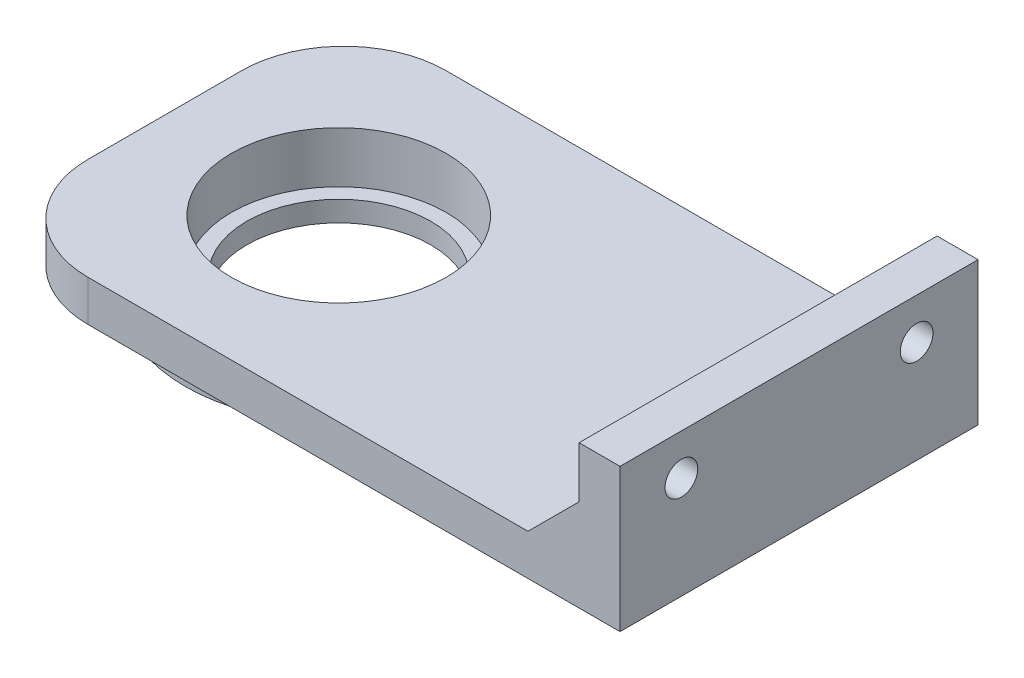
SolidWorks part; units mm, degrees
material "PET"
ref_plane "Спереди" through (0, 0, 0) normal (0, 0, 1) x (1, 0, 0)
ref_plane "Сверху" through (0, 0, 0) normal (0, 1, 0) x (1, 0, 0)
ref_plane "Справа" through (0, 0, 0) normal (1, 0, 0) x (0, 0, -1)
sketch "Эскиз1" plane through (0, 0, 0) normal (0, 1, 0) x (1, 0, 0)
  line L1 (31, -17.5) -> (-31, -17.5)
  line L2 (31, -17.5) -> (31, 17.5)
  line L3 (31, 17.5) -> (-31, 17.5)
  line L4 (-31, -17.5) -> (-31, 17.5)
  line L5 (31, -17.5) -> (-31, 17.5) construction
  line L6 (31, 17.5) -> (-31, -17.5) construction
  circle A0 centre (-14, 0) radius 10.5
  point P0 (0, 0)
  dimension "D4" = 21
  dimension "D1" = 62
  dimension "D2" = 35
  dimension "D3" = 17
extrude "Бобышка-Вытянуть1" add sketch "Эскиз1" along normal blind 4
sketch "Эскиз3" plane through (0, 0, 0) normal (0, 1, 0) x (1, 0, 0)
  circle A0 centre (-14, 0) radius 10.5 construction
  circle A1 centre (-14, 0) radius 10.5
  circle A2 centre (-14, 0) radius 15
  dimension "D1" = 30
extrude "Бобышка-Вытянуть2" add sketch "Эскиз3" along normal blind 5 and the other way blind 1
fillet "Скругление1" radius 10 2 edges at (-31, 2, 17.5) (-31, 2, -17.5)
sketch "Эскиз4" plane through (0, 4, 0) normal (0, 1, 0) x (1, 0, 0)
  line L0 (-21, -17.5) -> (31, -17.5) construction
  line L1 (31, 17.5) -> (27, 17.5)
  line L2 (31, 17.5) -> (31, -17.5)
  line L3 (31, -17.5) -> (27, -17.5)
  line L4 (27, 17.5) -> (27, -17.5)
  dimension "D1" = 4
extrude "Бобышка-Вытянуть3" add sketch "Эскиз4" along normal blind 10
chamfer "Фаска1" distance 5 angle 45 1 edges at (27, 4, 0)
sketch "Эскиз5" plane through (31, 0, 0) normal (1, 0, 0) x (0, 0, -1)
  line L0 (0, 0) -> (0, 16.3191) construction
  line L1 (-17.5, 14) -> (17.5, 14) construction
  circle A0 centre (-11.5, 10) radius 1.6
  circle A1 centre (11.5, 10) radius 1.6
  dimension "D1" = 3.2
  dimension "D2" = 23
  dimension "D3" = 4
extrude "Вырез-Вытянуть1" cut sketch "Эскиз5" against normal blind 25
sketch "Эскиз6" plane through (27, 0, 0) normal (-1, 0, 0) x (0, 0, 1)
  line L0 (0, 0) -> (0, 18.4599) construction
  circle A0 centre (-11.5, 10) radius 3
  circle A1 centre (11.5, 10) radius 3
  dimension "D1" = 6
extrude "Вырез-Вытянуть2" cut sketch "Эскиз6" along normal blind 25
sketch "Эскиз7" plane through (0, 0, 17.5) normal (0, 0, 1) x (1, 0, 0)
  line L1 (-31, 4) -> (2.2289, 4)
  line L2 (-31, 4) -> (-31, 6.6658)
  line L3 (-31, 6.6658) -> (2.2289, 6.6658)
  line L4 (2.2289, 4) -> (2.2289, 6.6658)
extrude "Вырез-Вытянуть3" cut sketch "Эскиз7" against normal blind 50
sketch "Эскиз8" plane through (0, -1, 0) normal (0, -1, 0) x (1, 0, 0)
  circle A2 centre (-14, 0) radius 9
  circle A3 centre (-14, 0) radius 15
  dimension "D2" = 18
extrude "Бобышка-Вытянуть4" add sketch "Эскиз8" along normal blind 2
